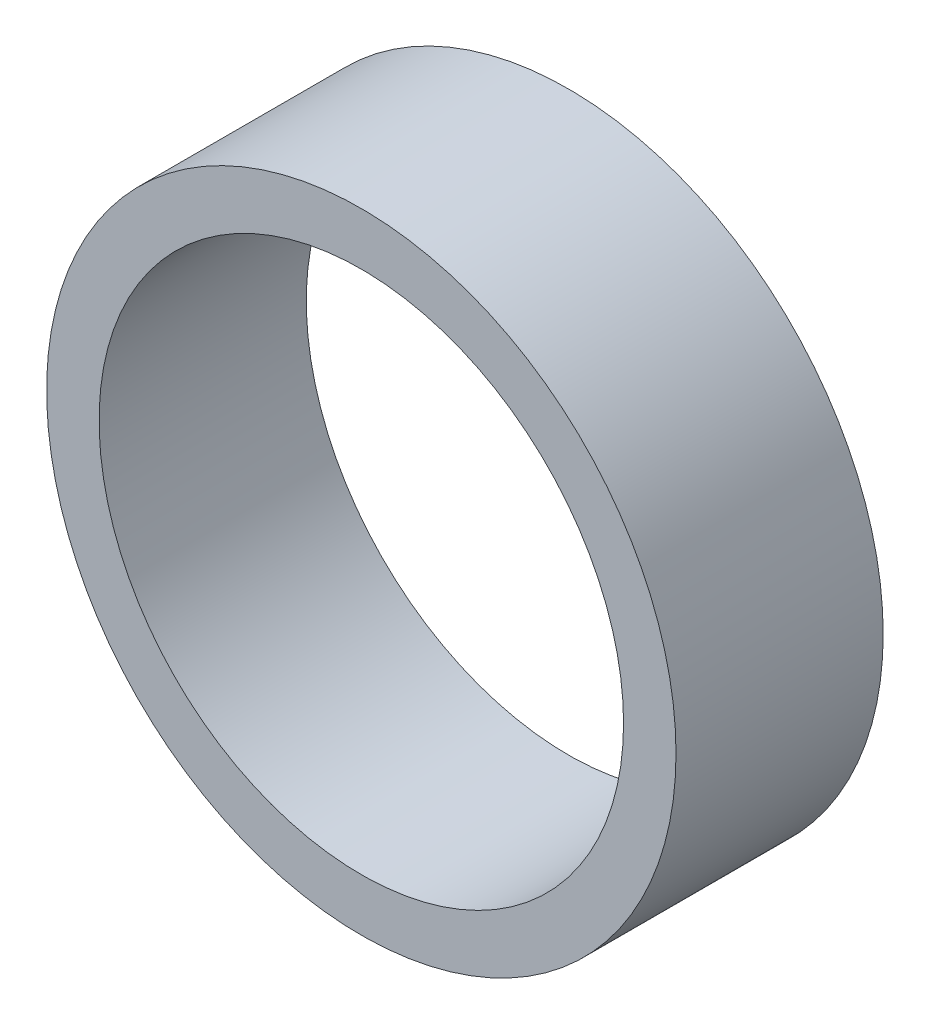
SolidWorks part; units mm, degrees
material "Brass"
ref_plane "Front Plane" through (0, 0, 0) normal (0, 0, 1) x (1, 0, 0)
ref_plane "Top Plane" through (0, 0, 0) normal (0, 1, 0) x (1, 0, 0)
ref_plane "Right Plane" through (0, 0, 0) normal (1, 0, 0) x (0, 0, -1)
sketch "Sketch1" plane through (0, 0, 0) normal (0, 0, 1) x (1, 0, 0)
  circle A0 centre (0, 0) radius 20
  circle A1 centre (0, 0) radius 24
  dimension "D1" = 40
  dimension "D2" = 4
extrude "Boss-Extrude1" add sketch "Sketch1" along normal blind 15.8
